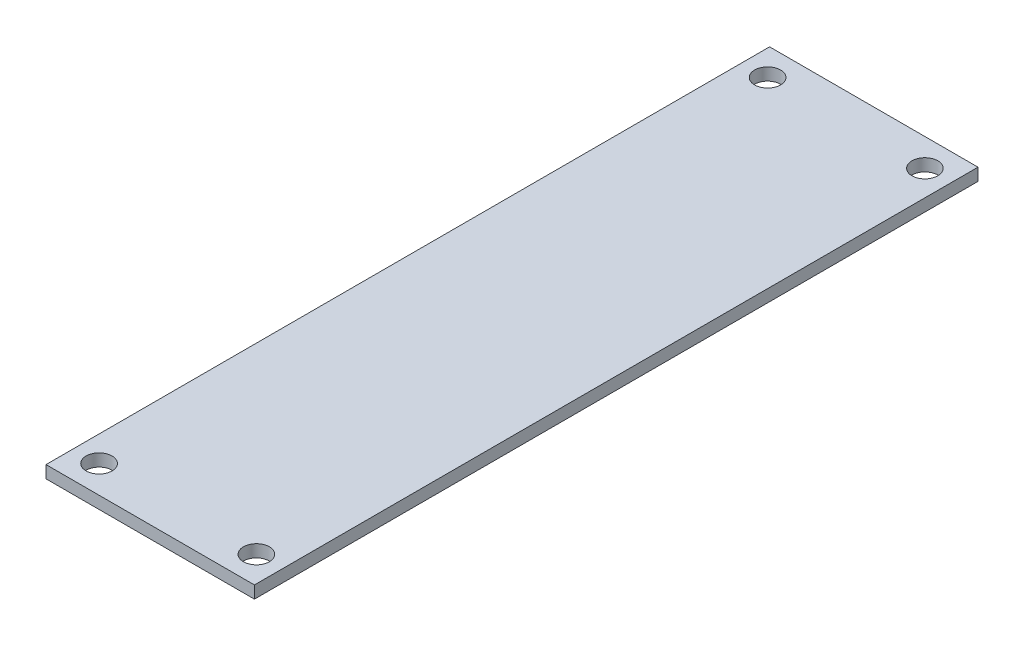
SolidWorks part; units mm, degrees
ref_plane "Front Plane" through (0, 0, 0) normal (0, 0, 1) x (1, 0, 0)
ref_plane "Top Plane" through (0, 0, 0) normal (0, 1, 0) x (1, 0, 0)
ref_plane "Right Plane" through (0, 0, 0) normal (1, 0, 0) x (0, 0, -1)
sketch "Sketch1" plane through (0, 0, 0) normal (0, 1, 0) x (1, 0, 0)
  line L0 (0, 46) -> (0, -46) construction
  line L1 (13.25, 46) -> (-13.25, 46)
  line L2 (13.25, 46) -> (13.25, -46)
  line L3 (13.25, -46) -> (-13.25, -46)
  line L4 (-13.25, 46) -> (-13.25, -46)
  line L5 (13.25, 46) -> (-13.25, -46) construction
  line L6 (13.25, -46) -> (-13.25, 46) construction
  line L7 (-13.25, 0) -> (13.25, 0) construction
  circle A0 centre (-10, 42.5) radius 1.65
  circle A1 centre (10, 42.5) radius 1.65
  circle A2 centre (10, -42.5) radius 1.65
  circle A3 centre (-10, -42.5) radius 1.65
  point P0 (0, 0)
  dimension "D3" = 3.3
  dimension "D1" = 26.5
  dimension "D2" = 92
  dimension "D4" = 20
  dimension "D5" = 85
extrude "Boss-Extrude1" add sketch "Sketch1" along normal blind 1.57
